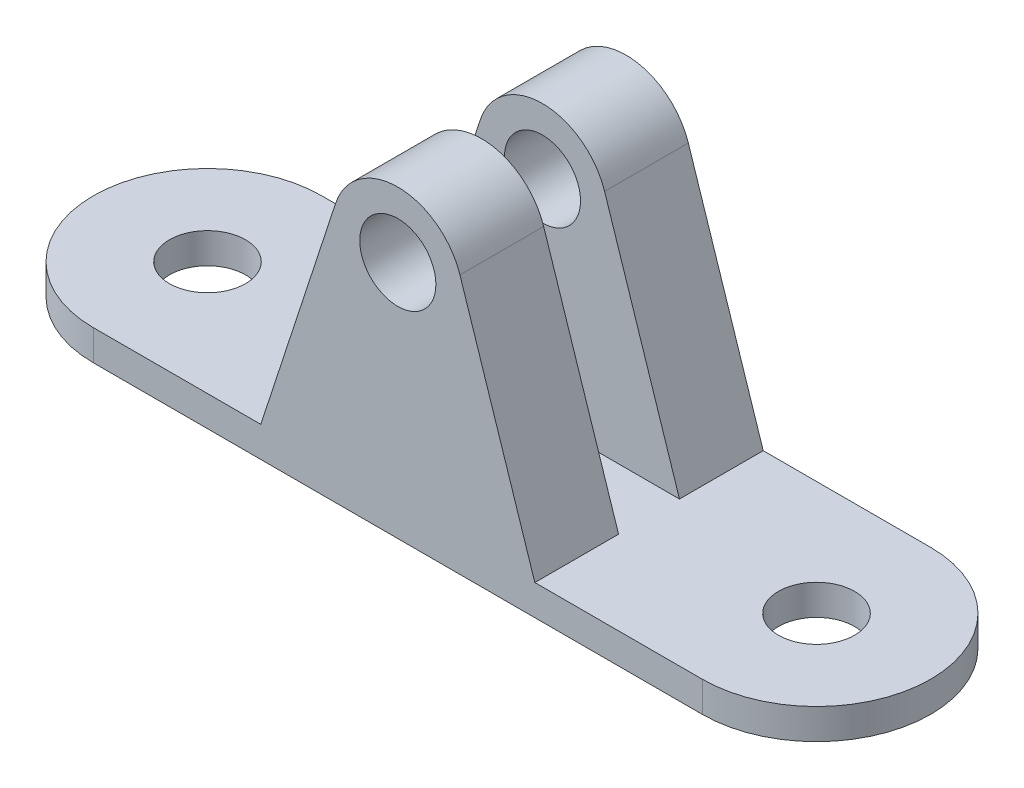
SolidWorks part; units mm, degrees
ref_plane "Front Plane" through (0, 0, 0) normal (0, 0, 1) x (1, 0, 0)
ref_plane "Top Plane" through (0, 0, 0) normal (0, 1, 0) x (1, 0, 0)
ref_plane "Right Plane" through (0, 0, 0) normal (1, 0, 0) x (0, 0, -1)
sketch "Sketch1" plane through (0, 0, 0) normal (0, 1, 0) x (1, 0, 0)
  line L0 (0, 0) -> (40, 0) construction
  line L1 (0, 7.5) -> (40, 7.5)
  line L2 (0, -7.5) -> (40, -7.5)
  arc A0 (0, 7.5) -> (0, -7.5) centre (0, 0) ccw
  arc A1 (40, -7.5) -> (40, 7.5) centre (40, 0) ccw
  point P3 (20, 0)
  dimension "D2" = 55
  dimension "D1" = 15
extrude "Boss-Extrude1" add sketch "Sketch1" along normal blind 2
sketch "Sketch2" plane through (0, 0, 7.5) normal (0, 0, 1) x (1, 0, 0)
  line L0 (20, 2) -> (20, 12.2927) construction
  line L1 (0, 2) -> (40, 2) construction
  line L2 (11, 2) -> (15.9188, 17.0407)
  line L3 (11, 2) -> (20, 2)
  line L4 (29, 2) -> (24.0812, 17.0407)
  arc A0 (15.9188, 17.0407) -> (24.0812, 17.0407) centre (20, 15.7061) cw
  circle A1 centre (20, 15.7061) radius 2.5
  dimension "D3" = 5
  dimension "D1" = 18
  dimension "D2" = 18
extrude "Boss-Extrude2" add sketch "Sketch2" against normal blind 5.5
ref_plane "Plane1" through (0, 0, 0) normal (0, 0, 1) x (1, 0, 0)
mirror "Mirror1" about plane through (0, 0, 0) normal (0, 0, 1) of "Boss-Extrude2"
sketch "Sketch3" plane through (0, 2, 0) normal (0, 1, 0) x (1, 0, 0)
  circle A0 centre (0, 0) radius 2.5
  circle A1 centre (40, 0) radius 2.5
  dimension "D1" = 5
extrude "Cut-Extrude1" cut sketch "Sketch3" against normal blind 2
